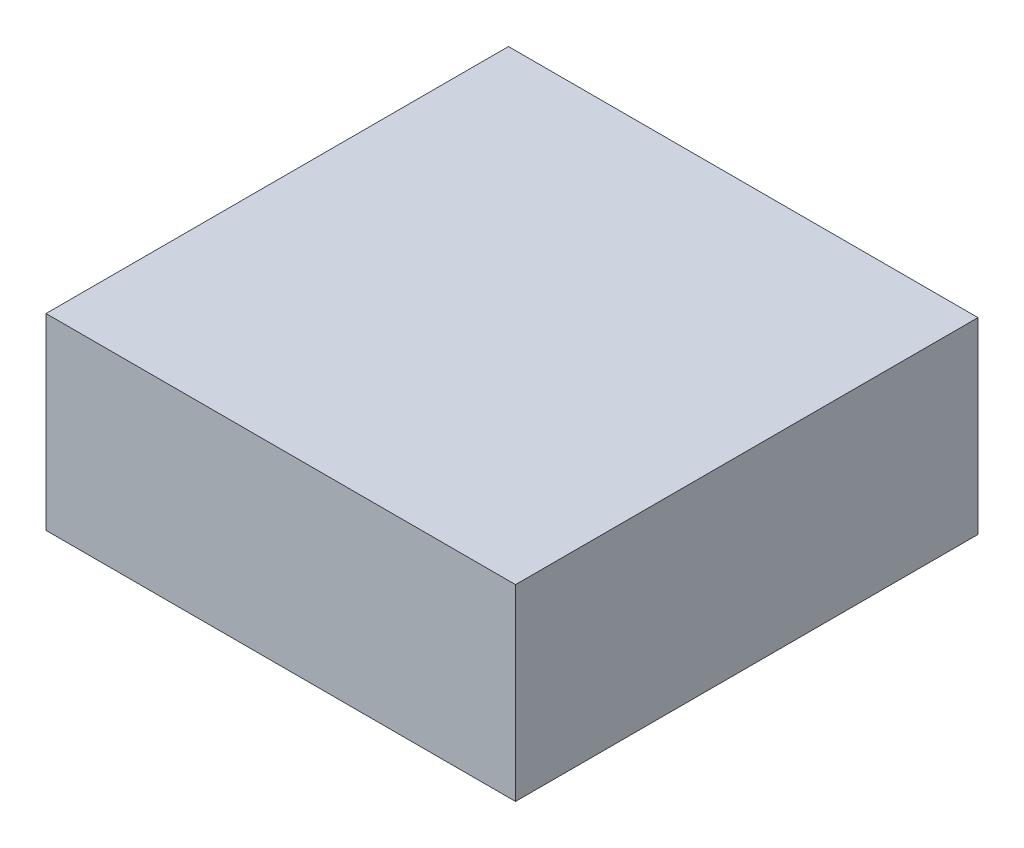
SolidWorks part; units mm, degrees
ref_plane "Front Plane" through (0, 0, 0) normal (0, 0, 1) x (1, 0, 0)
ref_plane "Top Plane" through (0, 0, 0) normal (0, 1, 0) x (1, 0, 0)
ref_plane "Right Plane" through (0, 0, 0) normal (1, 0, 0) x (0, 0, -1)
sketch "Sketch2" plane through (0, 0, 0) normal (0, 1, 0) x (1, 0, 0)
  line L1 (0, 0) -> (50.8, 0)
  line L2 (0, 0) -> (0, 50.038)
  line L3 (0, 50.038) -> (50.8, 50.038)
  line L4 (50.8, 0) -> (50.8, 50.038)
  dimension "D1" = 50.8
  dimension "D2" = 50.038
extrude "Boss-Extrude1" add sketch "Sketch2" along normal blind 20.32
